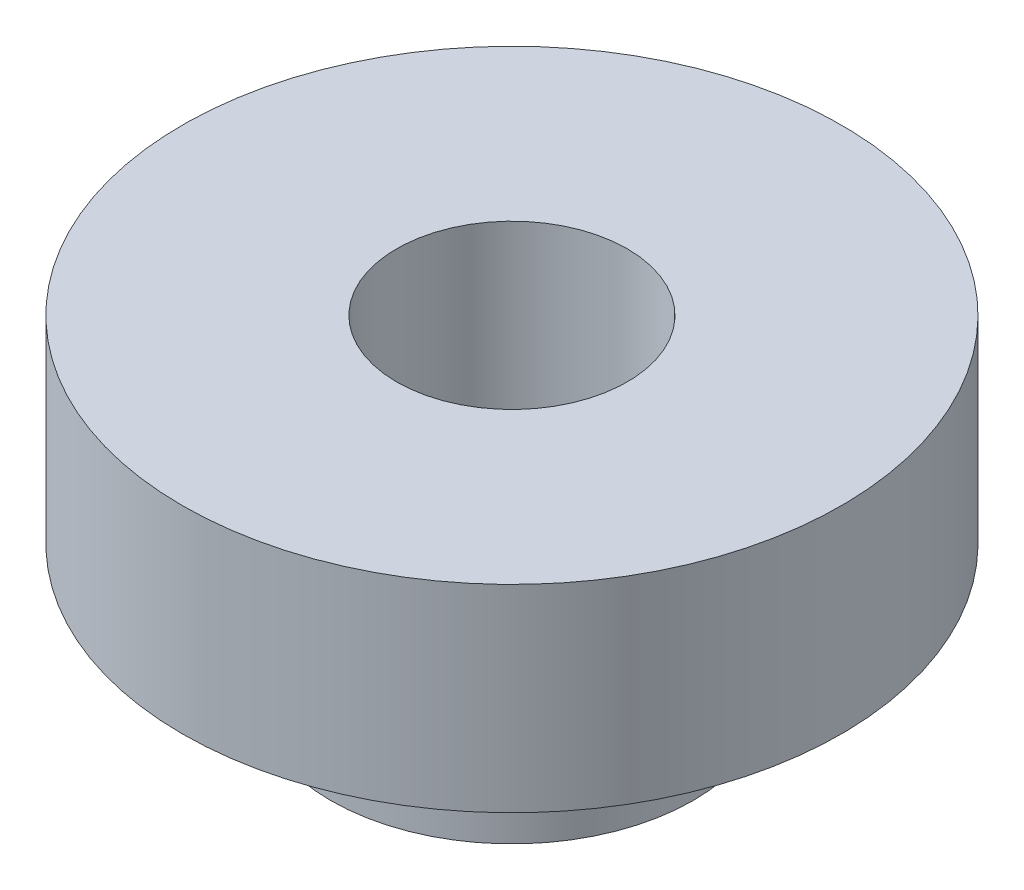
SolidWorks part; units mm, degrees
ref_plane "Front Plane" through (0, 0, 0) normal (0, 0, 1) x (1, 0, 0)
ref_plane "Top Plane" through (0, 0, 0) normal (0, 1, 0) x (1, 0, 0)
ref_plane "Right Plane" through (0, 0, 0) normal (1, 0, 0) x (0, 0, -1)
sketch "Sketch1" plane through (0, 0, 0) normal (0, 1, 0) x (1, 0, 0)
  line L0 (0, 0) -> (0, 57.15) construction
  circle A0 centre (0, 0) radius 57.15
  circle A1 centre (0, 6.35) radius 1.397
  circle A2 centre (0, 25.4) radius 3.175
  circle A3 centre (0, 50.8) radius 3.175
  circle A4 centre (25.4, 0) radius 3.175
  circle A5 centre (0, -25.4) radius 3.175
  circle A6 centre (-25.4, 0) radius 3.175
  circle A7 centre (6.35, 0) radius 1.397
  circle A8 centre (0, -6.35) radius 1.397
  circle A9 centre (-6.35, 0) radius 1.397
  circle A10 centre (35.921, 35.921) radius 3.175
  circle A11 centre (50.8, 0) radius 3.175
  circle A12 centre (35.921, -35.921) radius 3.175
  circle A13 centre (0, -50.8) radius 3.175
  circle A14 centre (-35.921, -35.921) radius 3.175
  circle A15 centre (-50.8, 0) radius 3.175
  circle A16 centre (-35.921, 35.921) radius 3.175
  point P19 (0, 0)
  point P26 (0, 0)
  point P40 (0, 0)
  dimension "D1" = 114.3
  dimension "D5" = 2.794
  dimension "D6" = 6.35
  dimension "D2" = 6.35
  dimension "D3" = 25.4
  dimension "D4" = 50.8
  dimension "D7" = 4
  dimension "D8" = 4
  dimension "D9" = 8
extrude "Boss-Extrude1" add sketch "Sketch1" along normal blind 4.572
sketch "Sketch2" plane through (0, 4.572, 0) normal (0, 1, 0) x (1, 0, 0)
  circle A0 centre (-25.4, 0) radius 2.75
  circle A1 centre (-25.4, 0) radius 1.75
  dimension "D1" = 3.5
  dimension "D2" = 5.5
extrude "Boss-Extrude2" add sketch "Sketch2" against normal blind 2 separate body
sketch "Sketch3" plane through (0, 4.572, 0) normal (0, 1, 0) x (1, 0, 0)
  circle A0 centre (-25.4, 0) radius 5
  circle A2 centre (-25.4, 0) radius 1.75 construction
  circle A3 centre (-25.4, 0) radius 1.75
  dimension "D1" = 10
extrude "Boss-Extrude3" add sketch "Sketch3" along normal blind 3
delete or keep bodies "Body-Delete/Keep 1" type keep bodies bodies 103
